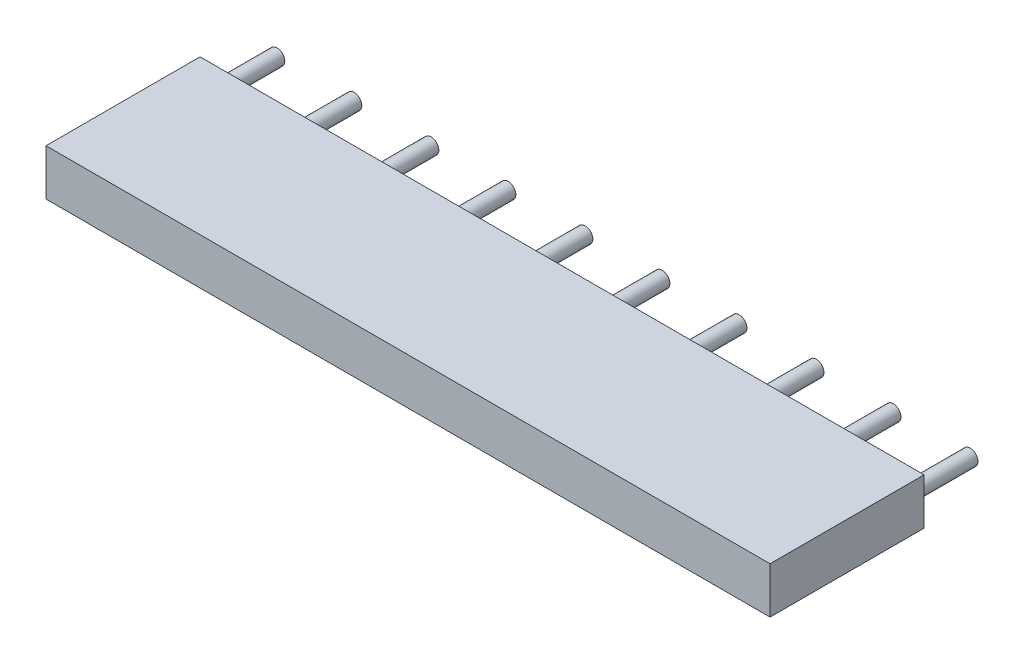
SolidWorks part; units mm, degrees
ref_plane "Front Plane" through (0, 0, 0) normal (0, 0, 1) x (1, 0, 0)
ref_plane "Top Plane" through (0, 0, 0) normal (0, 1, 0) x (1, 0, 0)
ref_plane "Right Plane" through (0, 0, 0) normal (1, 0, 0) x (0, 0, -1)
sketch "Sketch1" plane through (0, 0, 0) normal (0, 0, 1) x (1, 0, 0)
  line L0 (-0.5, 0.75) -> (-0.5, -0.75)
  line L1 (-0.5, -0.75) -> (23, -0.75)
  line L2 (23, -0.75) -> (23, 0.75)
  line L3 (23, 0.75) -> (-0.5, 0.75)
extrude "Component_Outline" add sketch "Sketch1" along normal blind 5 separate body
sketch "Sketch2" plane through (0, 0, 0) normal (0, 0, 1) x (1, 0, 0)
  circle A0 centre (0, 0) radius 0.25
extrude "1" add sketch "Sketch2" against normal blind 2 separate body
sketch "Sketch3" plane through (0, 0, 0) normal (0, 0, 1) x (1, 0, 0)
  circle A0 centre (2.5, 0) radius 0.25
extrude "2" add sketch "Sketch3" against normal blind 2 separate body
sketch "Sketch4" plane through (0, 0, 0) normal (0, 0, 1) x (1, 0, 0)
  circle A0 centre (5, 0) radius 0.25
extrude "3" add sketch "Sketch4" against normal blind 2 separate body
sketch "Sketch5" plane through (0, 0, 0) normal (0, 0, 1) x (1, 0, 0)
  circle A0 centre (7.5, 0) radius 0.25
extrude "4" add sketch "Sketch5" against normal blind 2 separate body
sketch "Sketch6" plane through (0, 0, 0) normal (0, 0, 1) x (1, 0, 0)
  circle A0 centre (10, 0) radius 0.25
extrude "5" add sketch "Sketch6" against normal blind 2 separate body
sketch "Sketch7" plane through (0, 0, 0) normal (0, 0, 1) x (1, 0, 0)
  circle A0 centre (12.5, 0) radius 0.25
extrude "6" add sketch "Sketch7" against normal blind 2 separate body
sketch "Sketch8" plane through (0, 0, 0) normal (0, 0, 1) x (1, 0, 0)
  circle A0 centre (15, 0) radius 0.25
extrude "7" add sketch "Sketch8" against normal blind 2 separate body
sketch "Sketch9" plane through (0, 0, 0) normal (0, 0, 1) x (1, 0, 0)
  circle A0 centre (17.5, 0) radius 0.25
extrude "8" add sketch "Sketch9" against normal blind 2 separate body
sketch "Sketch10" plane through (0, 0, 0) normal (0, 0, 1) x (1, 0, 0)
  circle A0 centre (20, 0) radius 0.25
extrude "9" add sketch "Sketch10" against normal blind 2 separate body
sketch "Sketch11" plane through (0, 0, 0) normal (0, 0, 1) x (1, 0, 0)
  circle A0 centre (22.5, 0) radius 0.25
extrude "10" add sketch "Sketch11" against normal blind 2 separate body
sketch3d "3DSketch1"
  line L0 (0, 0, 0) -> (1, 0, 0)
  line L1 (0, 0, 0) -> (0, 1, 0)
  line L2 (0, 0, 0) -> (0, 0, 1)
  point P0 (0, 0, 0)
